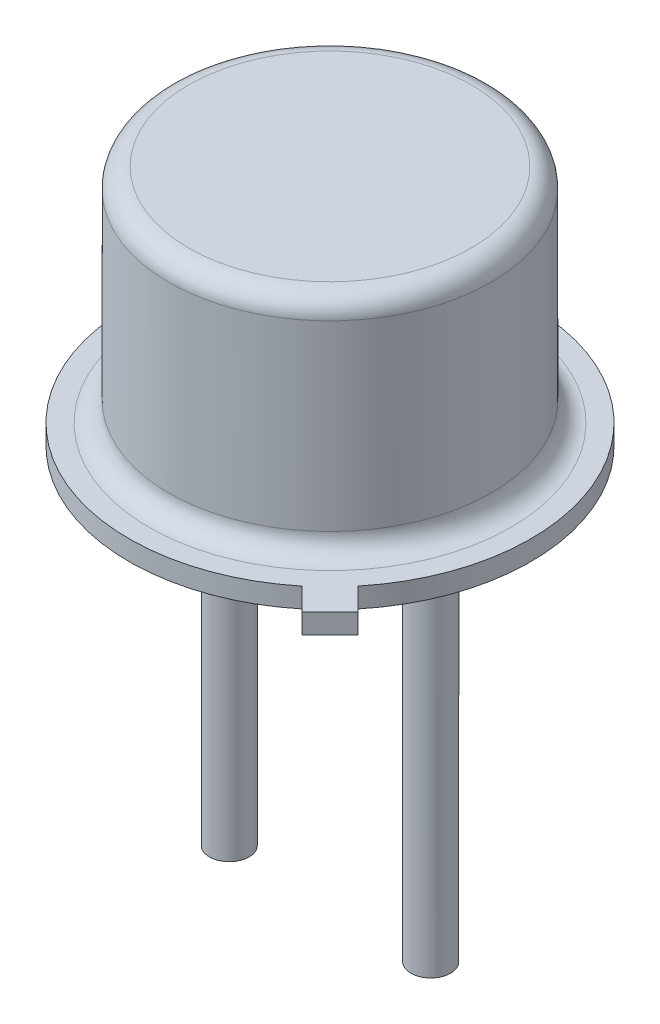
SolidWorks part; units mm, degrees
ref_plane "Front Plane" through (0, 0, 0) normal (0, 0, 1) x (1, 0, 0)
ref_plane "Top Plane" through (0, 0, 0) normal (0, 1, 0) x (1, 0, 0)
ref_plane "Right Plane" through (0, 0, 0) normal (1, 0, 0) x (0, 0, -1)
ref_plane "Plane1" through (0, 4.06, 0) normal (0, 1, 0) x (-1, 0, 0)
sketch "sketch" plane through (0, 4.06, 0) normal (0, 1, 0) x (1, 0, 0)
  circle A0 centre (-2.54, 0) radius 4.064
extrude "Body" add sketch "sketch" along normal blind 6.1
sketch "Sketch1" plane through (0, 4.06, 0) normal (0, -1, 0) x (1, 0, 0)
  line L0 (-2.54, 4.6004) -> (-2.54, -4.8049) construction
  line L1 (0, 0) -> (-2.54, 0) construction
  circle A0 centre (0, 0) radius 0.5
  circle A1 centre (-2.54, -2.54) radius 0.5
  circle A2 centre (-5.08, 0) radius 0.5
  dimension "D2" = 1
  dimension "D1" = 2.54
extrude "Legs" add sketch "Sketch1" along normal blind 10
sketch "Sketch3" plane through (0, 4.06, 0) normal (0, -1, 0) x (1, 0, 0)
  line L0 (-2.54, 0) -> (1.5897, 4.1297) construction
  line L1 (1.2361, 4.4832) -> (1.9432, 3.7761)
  line L2 (1.2361, 4.4832) -> (0.6704, 3.9176)
  line L4 (1.9432, 3.7761) -> (1.3776, 3.2104)
  line L5 (-7.7147, 0) -> (2.4291, 0) construction
  arc A0 (0.6704, 3.9176) -> (1.3776, 3.2104) centre (-2.54, 0) ccw
  circle A1 centre (-2.54, 0) radius 4.064 construction
  dimension "D1" = 10.13
  dimension "D2" = 0.8
  dimension "D3" = 1
  dimension "D4" = 45
extrude "Lip" add sketch "Sketch3" against normal blind 0.5
fillet "Fillet2" radius 0.5 2 edges at (-2.54, 4.56, -4.064) (-2.54, 10.16, 4.064)
ref_plane "Board Plane" through (0, 2, 0) normal (0, 1, 0) x (-1, 0, 0)
sketch "Component_Outline" plane through (0, 2, 0) normal (0, 1, 0) x (-1, 0, 0)
  line L0 (-0.6704, 3.9176) -> (-1.2361, 4.4832)
  line L1 (-1.2361, 4.4832) -> (-1.9432, 3.7761)
  line L2 (-1.9432, 3.7761) -> (-1.3776, 3.2104)
  arc A0 (-1.3776, 3.2104) -> (-0.6704, 3.9176) centre (2.54, 0) ccw
  arc A1 (-1.3776, 3.2104) -> (-0.6704, 3.9176) centre (2.54, 0) ccw construction
